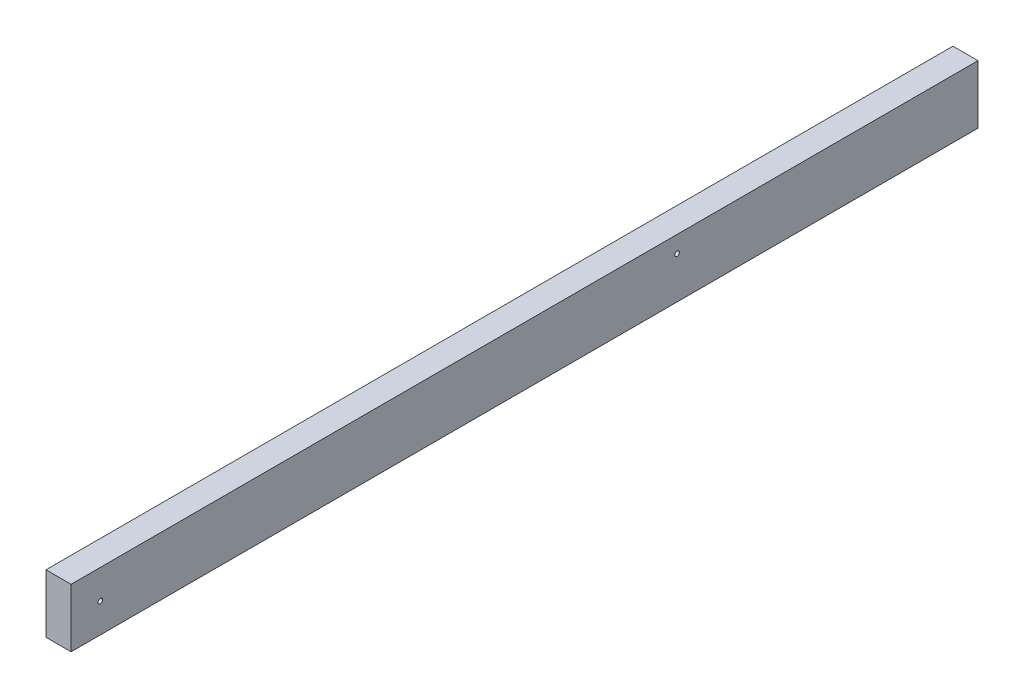
SolidWorks part; units mm, degrees
material "Pine"
ref_plane "Front Plane" through (0, 0, 0) normal (0, 0, 1) x (1, 0, 0)
ref_plane "Top Plane" through (0, 0, 0) normal (0, 1, 0) x (1, 0, 0)
ref_plane "Right Plane" through (0, 0, 0) normal (1, 0, 0) x (0, 0, -1)
sketch "Sketch1" plane through (0, 0, 0) normal (0, 0, 1) x (1, 0, 0)
  line L1 (-19.05, -44.45) -> (19.05, -44.45)
  line L2 (-19.05, -44.45) -> (-19.05, 44.45)
  line L3 (-19.05, 44.45) -> (19.05, 44.45)
  line L4 (19.05, -44.45) -> (19.05, 44.45)
  line L5 (-19.05, -44.45) -> (19.05, 44.45) construction
  line L6 (-19.05, 44.45) -> (19.05, -44.45) construction
  point P0 (0, 0)
  dimension "D1" = 88.9
  dimension "D2" = 38.1
extrude "Boss-Extrude1" add sketch "Sketch1" along normal blind 1377.95
sketch "Sketch2" plane through (19.05, 0, 0) normal (1, 0, 0) x (0, 0, -1)
  line L0 (-1377.95, -44.45) -> (-1377.95, 44.45) construction
  point P0 (-1333.5, 0)
  point P1 (-457.2, 19.05)
  point P5 (0, 0)
  point P6 (-457.7201, 30.1879)
  dimension "D1" = 920.75
  dimension "D2" = 44.45
  dimension "D3" = 19.05
hole_wizard "9/32 (0.28125) Diameter Hole1" positions "Sketch3" profile "Sketch4" hole size "9/32" standard "ANSI Inch" end condition through all
sketch "Sketch3" plane through (19.05, 0, 0) normal (1, 0, 0) x (0, 0, -1)
  point P0 (-1333.5, 0)
  point P3 (-457.2, 19.05)
sketch "Sketch4" plane through (19.05, 0, 1333.5) normal (0, 1, 0) x (0, 0, -1)
  line L0 (0, 0) -> (0, 38.1)
  line L1 (0, 38.1) -> (3.5719, 38.1)
  line L2 (3.5719, 38.1) -> (3.5719, 0)
  line L5 (3.5719, 0) -> (0, 0)
  line L11 (0, -6.35) -> (0, 107.95) construction
  dimension "Thru Hole Dia." = 7.1437
  dimension "Thru Hole Depth" = 38.1
